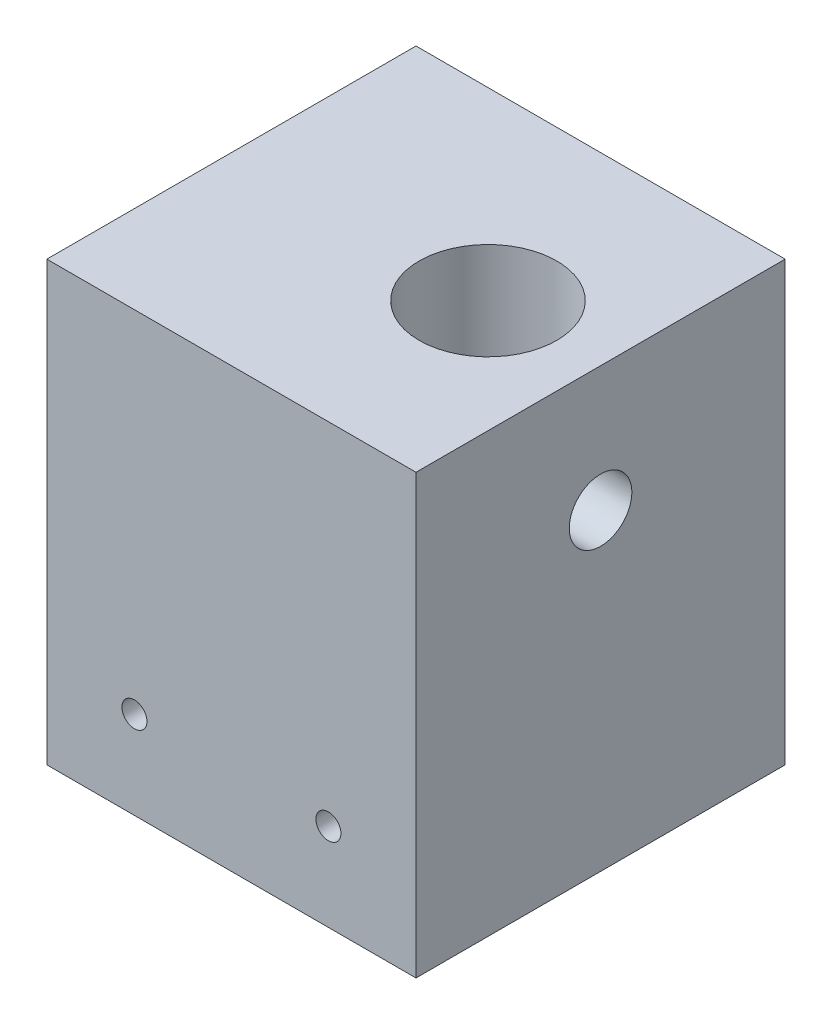
SolidWorks part; units mm, degrees
ref_plane "Plan de face" through (0, 0, 0) normal (0, 0, 1) x (1, 0, 0)
ref_plane "Plan de dessus" through (0, 0, 0) normal (0, 1, 0) x (1, 0, 0)
ref_plane "Plan de droite" through (0, 0, 0) normal (1, 0, 0) x (0, 0, -1)
sketch "Esquisse1" plane through (0, 0, 0) normal (0, 1, 0) x (1, 0, 0)
  line L1 (-29.291, 17.4415) -> (29.709, 17.4415)
  line L2 (-29.291, 17.4415) -> (-29.291, -41.5585)
  line L3 (-29.291, -41.5585) -> (29.709, -41.5585)
  line L4 (29.709, 17.4415) -> (29.709, -41.5585)
  dimension "D1" = 59
  dimension "D2" = 59
extrude "Boss.-Extru.1" add sketch "Esquisse1" along normal blind 70
sketch "Esquisse2" plane through (0, 0, 41.5585) normal (0, 0, 1) x (1, 0, 0)
  line L0 (29.709, 14) -> (15.709, 14) construction
  line L1 (29.709, 70) -> (29.709, 0) construction
  line L2 (15.709, 14) -> (-15.291, 14) construction
  line L3 (-15.291, 14) -> (-29.291, 14) construction
  line L4 (-29.291, 70) -> (-29.291, 0) construction
  line L5 (15.709, 14) -> (15.709, 0) construction
  line L6 (-29.291, 0) -> (29.709, 0) construction
  line L7 (-15.291, 14) -> (-15.291, 0) construction
  circle A0 centre (-15.291, 14) radius 2
  circle A1 centre (15.709, 14) radius 2
  dimension "D1" = 4
  dimension "D2" = 14
extrude "Enlèv. mat.-Extru.1" cut sketch "Esquisse2" against normal up to next
sketch "Esquisse3" plane through (0, 70, 0) normal (0, 1, 0) x (1, 0, 0)
  line L0 (11.709, -41.5585) -> (11.709, -12.0585) construction
  line L1 (-29.291, -41.5585) -> (29.709, -41.5585) construction
  line L2 (11.709, -12.0585) -> (11.709, 17.4415) construction
  line L3 (29.709, 17.4415) -> (-29.291, 17.4415) construction
  line L4 (11.709, -12.0585) -> (29.709, -12.0585) construction
  line L5 (29.709, -41.5585) -> (29.709, 17.4415) construction
  circle A0 centre (11.709, -12.0585) radius 11
  dimension "D2" = 22
  dimension "D1" = 18
extrude "Enlèv. mat.-Extru.2" cut sketch "Esquisse3" against normal blind 25
sketch "Esquisse4" plane through (29.709, 0, 0) normal (1, 0, 0) x (0, 0, -1)
  line L0 (-41.5585, 50) -> (-12.0585, 50) construction
  line L1 (-41.5585, 70) -> (-41.5585, 0) construction
  line L2 (-12.0585, 50) -> (17.4415, 50) construction
  line L3 (17.4415, 70) -> (17.4415, 0) construction
  line L4 (-12.0585, 50) -> (-12.0585, 70) construction
  line L5 (-41.5585, 70) -> (17.4415, 70) construction
  circle A0 centre (-12.0585, 50) radius 5
  dimension "D2" = 10
  dimension "D1" = 20
extrude "Enlèv. mat.-Extru.3" cut sketch "Esquisse4" against normal up to next
